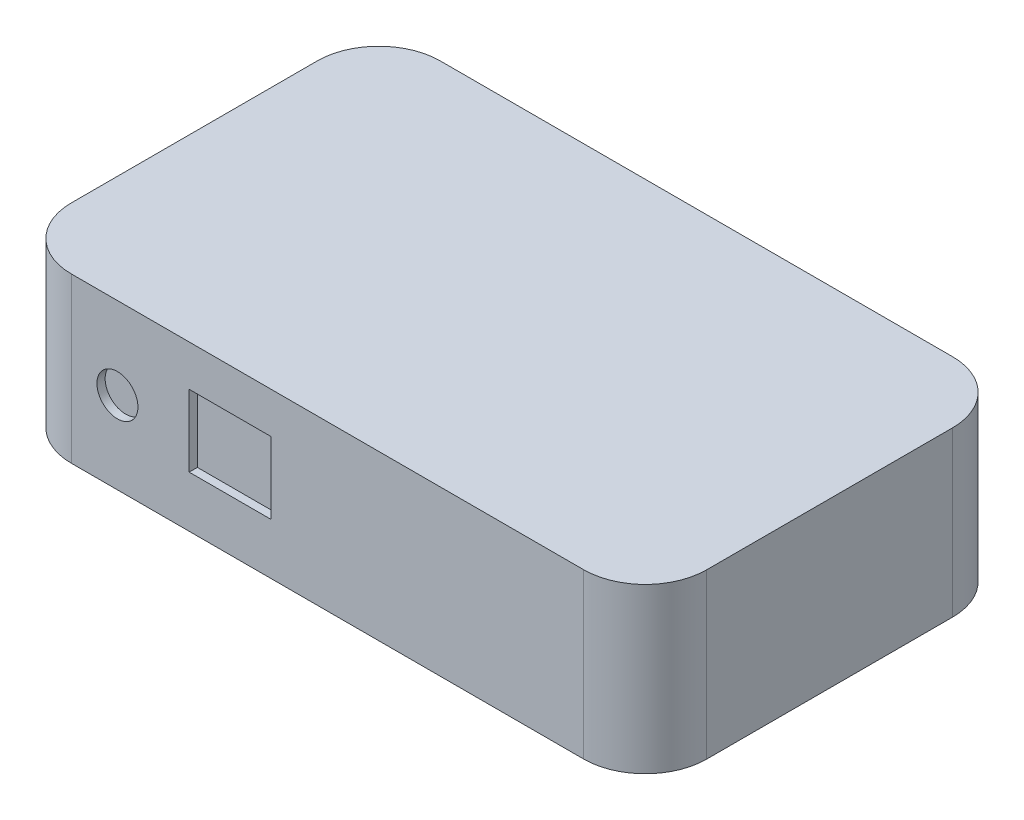
SolidWorks part; units mm, degrees
material "Delrin 2700 NC010, Low Viscosity Acetal Copolymer (SS)"
ref_plane "Front Plane" through (0, 0, 0) normal (0, 0, 1) x (1, 0, 0)
ref_plane "Top Plane" through (0, 0, 0) normal (0, 1, 0) x (1, 0, 0)
ref_plane "Right Plane" through (0, 0, 0) normal (1, 0, 0) x (0, 0, -1)
sketch "Sketch1" plane through (0, 0, 0) normal (0, 1, 0) x (1, 0, 0)
  line L0 (-49.2125, 28.575) -> (49.2125, -28.575) construction
  line L1 (-49.2125, 28.575) -> (49.2125, 28.575)
  line L2 (-49.2125, 28.575) -> (-49.2125, -28.575)
  line L3 (-49.2125, -28.575) -> (49.2125, -28.575)
  line L4 (49.2125, 28.575) -> (49.2125, -28.575)
  dimension "D1" = 57.15
  dimension "D2" = 98.425
extrude "Boss-Extrude1" add sketch "Sketch1" along normal blind 25.4
sketch "Sketch2" plane through (0, 0, 0) normal (0, -1, 0) x (1, 0, 0)
  line L0 (-37.7825, 0) -> (37.7825, 0) construction
  line L1 (-42.8625, 22.86) -> (-37.7825, 22.86)
  line L2 (-42.8625, 22.86) -> (-42.8625, -22.86)
  line L3 (-42.8625, -22.86) -> (-37.7825, -22.86)
  line L4 (-37.7825, 22.86) -> (-37.7825, -22.86)
  line L5 (37.7825, 22.86) -> (42.8625, 22.86)
  line L6 (37.7825, 22.86) -> (37.7825, -22.86)
  line L7 (37.7825, -22.86) -> (42.8625, -22.86)
  line L8 (42.8625, 22.86) -> (42.8625, -22.86)
  dimension "D1" = 45.72
  dimension "D2" = 5.08
  dimension "D3" = 85.725
extrude "Boss-Extrude2" add sketch "Sketch2" along normal blind 0.762
fillet "Fillet1" radius 9.525 4 edges at (49.2125, 12.7, -28.575) (-49.2125, 12.7, -28.575) (-49.2125, 12.7, 28.575) (49.2125, 12.7, 28.575)
sketch "Sketch3" plane through (0, 0, -28.575) normal (0, 0, -1) x (-1, 0, 0)
  line L0 (-30.9562, 7.9375) -> (-26.5906, 7.9375) construction
  line L1 (-38.1, 22.225) -> (-30.9562, 22.225)
  line L2 (-38.1, 22.225) -> (-38.1, 7.9375)
  line L3 (-38.1, 7.9375) -> (-30.9562, 7.9375)
  line L4 (-30.9562, 22.225) -> (-30.9562, 7.9375)
  line L5 (-26.5906, 22.225) -> (-19.4469, 22.225)
  line L6 (-26.5906, 22.225) -> (-26.5906, 7.9375)
  line L7 (-26.5906, 7.9375) -> (-19.4469, 7.9375)
  line L8 (-19.4469, 22.225) -> (-19.4469, 7.9375)
  line L9 (-15.0812, 22.225) -> (-7.9375, 22.225)
  line L10 (-15.0812, 22.225) -> (-15.0812, 7.9375)
  line L11 (-15.0812, 7.9375) -> (-7.9375, 7.9375)
  line L12 (-7.9375, 22.225) -> (-7.9375, 7.9375)
  line L13 (-3.5719, 22.225) -> (3.5719, 22.225)
  line L14 (-3.5719, 22.225) -> (-3.5719, 7.9375)
  line L15 (-3.5719, 7.9375) -> (3.5719, 7.9375)
  line L16 (3.5719, 22.225) -> (3.5719, 7.9375)
  line L17 (7.9375, 22.225) -> (15.0813, 22.225)
  line L18 (7.9375, 22.225) -> (7.9375, 7.9375)
  line L19 (7.9375, 7.9375) -> (15.0813, 7.9375)
  line L20 (15.0813, 22.225) -> (15.0813, 7.9375)
  line L21 (19.4469, 22.225) -> (26.5906, 22.225)
  line L22 (19.4469, 22.225) -> (19.4469, 7.9375)
  line L23 (19.4469, 7.9375) -> (26.5906, 7.9375)
  line L24 (26.5906, 22.225) -> (26.5906, 7.9375)
  line L25 (30.9563, 22.225) -> (38.1, 22.225)
  line L26 (30.9563, 22.225) -> (30.9563, 7.9375)
  line L27 (30.9563, 7.9375) -> (38.1, 7.9375)
  line L28 (38.1, 22.225) -> (38.1, 7.9375)
  line L29 (-19.4469, 7.9375) -> (-15.0812, 7.9375) construction
  line L30 (-7.9375, 7.9375) -> (-3.5719, 7.9375) construction
  line L31 (3.5719, 7.9375) -> (7.9375, 7.9375) construction
  line L32 (15.0813, 7.9375) -> (19.4469, 7.9375) construction
  line L33 (26.5906, 7.9375) -> (30.9563, 7.9375) construction
  line L34 (-39.6875, 25.4) -> (39.6875, 25.4) construction
  line L35 (-38.1, 7.9375) -> (-39.6875, 7.9375) construction
  line L36 (-39.6875, 25.4) -> (-39.6875, 0) construction
  line L37 (38.1, 7.9375) -> (39.6875, 7.9375) construction
  line L38 (39.6875, 0) -> (39.6875, 25.4) construction
  dimension "D1" = 7.1437
  dimension "D2" = 76.2
  dimension "D3" = 3.175
  dimension "D4" = 14.2875
extrude "Cut-Extrude1" cut sketch "Sketch3" against normal blind 1.27
sketch "Sketch4" plane through (0, 0, 28.575) normal (0, 0, 1) x (1, 0, 0)
  line L0 (-39.6875, 25.4) -> (39.6875, 25.4) construction
  line L1 (-21.4313, 19.05) -> (-8.7313, 19.05)
  line L2 (-21.4313, 19.05) -> (-21.4312, 7.9375)
  line L3 (-21.4312, 7.9375) -> (-8.7313, 7.9375)
  line L4 (-8.7313, 19.05) -> (-8.7313, 7.9375)
  line L5 (-49.2125, 0) -> (-49.2125, 25.4) construction
  circle A0 centre (-32.5438, 12.7) radius 3.175
  dimension "D5" = 6.35
  dimension "D1" = 12.7
  dimension "D2" = 11.1125
  dimension "D3" = 6.35
  dimension "D4" = 27.7812
  dimension "D6" = 12.7
  dimension "D7" = 11.1125
extrude "Cut-Extrude2" cut sketch "Sketch4" against normal blind 1.27
